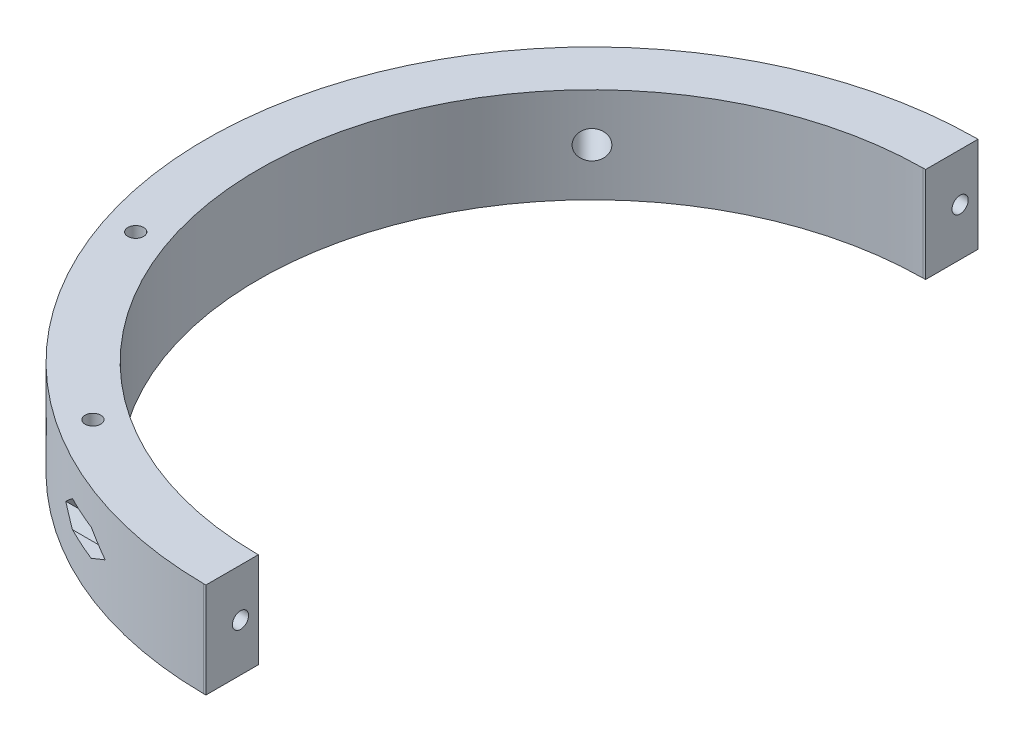
SolidWorks part; units mm, degrees
ref_plane "Front Plane" through (0, 0, 0) normal (0, 0, 1) x (1, 0, 0)
ref_plane "Top Plane" through (0, 0, 0) normal (0, 1, 0) x (1, 0, 0)
ref_plane "Right Plane" through (0, 0, 0) normal (1, 0, 0) x (0, 0, -1)
sketch "Sketch1" plane through (0, 0, 0) normal (0, 1, 0) x (1, 0, 0)
  line L0 (0, 70) -> (0, 81)
  line L1 (0, -70) -> (0, -81)
  circle A0 centre (0, 0) radius 70 construction
  arc A1 (0, 70) -> (0, -70) centre (0, 0) ccw
  arc A2 (0, -81) -> (0, 81) centre (0, 0) cw
  dimension "D1" = 140
  dimension "D2" = 11
extrude "Boss-Extrude1" add sketch "Sketch1" along normal mid plane 20 contours A1 L1 A2 L0
sketch "Sketch2" plane through (0, 0, 0) normal (1, 0, 0) x (0, 0, -1)
  line L1 (-81, 10) -> (81, 10)
  line L2 (-81, 10) -> (-81, -10)
  line L3 (-81, -10) -> (81, -10)
  line L4 (81, 10) -> (81, -10)
  line L5 (-81, 10) -> (81, -10) construction
  line L6 (-81, -10) -> (81, 10) construction
  point P0 (0, 0)
extrude "Cut-Extrude1" cut sketch "Sketch2" against normal blind 0.5
ref_plane "Plane1" through (-75, 0, 0) normal (1, 0, 0) x (0, 0, -1)
sketch "Sketch4" plane through (-75, 0, 0) normal (1, 0, 0) x (0, 0, -1)
  line L0 (44.55, 0) -> (-44.55, 0) construction
  line L1 (-72.1172, 2.825) -> (-75.3792, 2.825)
  line L2 (-75.3792, 2.825) -> (-77.0102, 0)
  line L3 (-77.0102, 0) -> (-75.3792, -2.825)
  line L4 (-75.3792, -2.825) -> (-72.1172, -2.825)
  line L5 (-72.1172, -2.825) -> (-70.4862, 0)
  line L6 (-70.4862, 0) -> (-72.1172, 2.825)
  line L8 (80.5105, 0) -> (78.8795, 2.825)
  line L9 (78.8795, 2.825) -> (75.6174, 2.825)
  line L10 (75.6174, 2.825) -> (73.9864, 0)
  line L11 (73.9864, 0) -> (75.6174, -2.825)
  line L12 (75.6174, -2.825) -> (78.8795, -2.825)
  line L13 (78.8795, -2.825) -> (80.5105, 0)
  line L14 (-69.9982, 10) -> (-69.9982, -10) construction
  line L16 (80.9985, 10) -> (80.9985, -10) construction
  circle A0 centre (-73.7482, 0) radius 2.825 construction
  circle A1 centre (77.2485, 0) radius 2.825 construction
  dimension "D1" = 5.65
  dimension "D2" = 3.75
  dimension "D3" = 3.75
extrude "Cut-Extrude2" cut sketch "Sketch4" along normal blind 67.5
hole_wizard "CBORE for M3 SHCS1" [suppressed] positions "Sketch6" profile "Sketch8" counterbore size "M3" standard "ANSI Metric"
sketch "Sketch6" [suppressed] plane through (-75, 0, 0) normal (1, 0, 0) x (0, 0, -1)
  line L0 (44.55, 0) -> (-44.55, 0) construction
  line L1 (-80.9985, -10) -> (-80.9985, 10) construction
  line L2 (80.9985, 10) -> (80.9985, -10) construction
  point P0 (-77.2485, 0)
  point P4 (77.2485, 0)
  dimension "D1" = 3.75
  dimension "D2" = 3.75
sketch "Sketch8" plane through (-75, 0, 77.2485) normal (0, 1, 0) x (0, 0, 1)
  line L0 (0, 0) -> (0, 95.5215)
  line L1 (0, 95.5215) -> (1.7, 94.5)
  line L2 (1.7, 94.5) -> (1.7, 67.5)
  line L3 (1.7, 67.5) -> (3.25, 67.5)
  line L4 (3.25, 67.5) -> (3.25, 0)
  line L5 (3.25, 0) -> (0, 0)
  line L10 (0, 95.5215) -> (-1.7, 94.5) construction
  line L11 (0, -6.35) -> (0, 107.95) construction
  dimension "Hole Dia." = 3.4
  dimension "Hole Depth" = 94.5
  dimension "C'Bore Dia." = 6.5
  dimension "C'Bore Depth" = 67.5
  dimension "Drill Angle" = 118
ref_plane "Plane2" through (-57.2756, 0, -57.2756) normal (-0.7071, 0, -0.7071) x (0, -1, 0)
ref_plane "Plane3" through (-57.2756, 0, 57.2756) normal (-0.7071, 0, 0.7071) x (0, -1, 0)
ref_plane "Plane4" through (0, 0, 0) normal (0.7071, 0, -0.7071) x (-0.7071, 0, -0.7071)
ref_plane "Plane5" through (0, 0, 0) normal (0.7071, 0, 0.7071) x (0.7071, 0, -0.7071)
ref_plane "Plane6" through (-49.4975, 0, -49.4975) normal (0.7071, 0, 0.7071) x (0, -1, 0)
hole_wizard "CBORE for M3 Pan Head Machine Screw4" [suppressed] positions "Sketch11" profile "Sketch12" counterbore size "M3" standard "ANSI Metric"
sketch "Sketch11" plane through (0, 0, 0) normal (0.7071, 0, 0.7071) x (0.7071, 0, -0.7071)
  point P0 (0, 0)
sketch "Sketch12" plane through (0, 0, 0) normal (0, 1, 0) x (0.7071, 0, -0.7071)
  line L0 (0, 0) -> (0, 114.5502)
  line L1 (0, 114.5502) -> (1.6, 114.5502)
  line L3 (1.6, 114.5502) -> (1.6, 73)
  line L4 (1.6, 73) -> (3.5, 73)
  line L5 (3.5, 73) -> (3.5, 0)
  line L7 (3.5, 0) -> (0, 0)
  line L11 (0, -6.35) -> (0, 107.95) construction
  dimension "Thru Hole Dia." = 3.2
  dimension "Thru Hole Depth" = 114.5502
  dimension "C'Bore Dia." = 7
  dimension "C'Bore Depth" = 73
sketch "Sketch15" [suppressed] plane through (-57.2756, 0, -57.2756) normal (-0.7071, 0, -0.7071) x (0, -1, 0)
  line L0 (0, -5.85) -> (0, 2761.2985) construction
  line L1 (-0.5, -5.85) -> (-4.25, -5.85)
  line L2 (-4.25, -5.85) -> (-6.95, 1.8)
  line L3 (-0.5, -5.85) -> (-0.5, -1) construction
  line L4 (-0.5, 1) -> (-0.5, 2.63) construction
  line L5 (0, 3.13) -> (0, 37.67)
  line L6 (-6.95, 1.8) -> (-4.4104, 32.0511)
  line L7 (0, 3.13) -> (0, -5.85)
  line L8 (0, -5.85) -> (-0.5, -5.85)
  arc A0 (-0.5, -1) -> (-0.5, 1) centre (-0.5, 0) cw construction
  arc A1 (-0.5, 2.63) -> (0, 3.13) centre (0, 2.63) cw construction
  arc A2 (-4.4104, 32.0511) -> (0, 37.67) centre (2.0668, 31.5074) cw
extrude "Cut-Extrude4" [suppressed] cut sketch "Sketch15" against normal blind 6
mirror "Mirror1" [suppressed] about plane through (0, 0, 0) normal (0, 1, 0)
hole_wizard "Ø6.0mm Dowel Hole2" positions "Sketch18" profile "Sketch19" hole size "Ø6.0" standard "ANSI Metric" end condition through all
sketch "Sketch18" plane through (0, 0, 0) normal (0.7071, 0, -0.7071) x (-0.7071, 0, -0.7071)
  point P0 (0, 0)
sketch "Sketch19" plane through (0, 0, 0) normal (0, 1, 0) x (-0.7071, 0, -0.7071)
  line L0 (0, 0) -> (0, 114.5502)
  line L1 (0, 114.5502) -> (2.95, 114.5502)
  line L2 (2.95, 114.5502) -> (2.95, 0)
  line L5 (2.95, 0) -> (0, 0)
  line L11 (0, -6.35) -> (0, 107.95) construction
  dimension "Thru Hole Dia." = 5.9
  dimension "Thru Hole Depth" = 114.5502
hole_wizard "Ø6.0mm Dowel Hole3" [suppressed] positions "Sketch20" profile "Sketch21" hole size "Ø6.0" standard "ANSI Metric"
sketch "Sketch20" plane through (0, 0, 0) normal (0.7071, 0, -0.7071) x (-0.7071, 0, -0.7071)
  point P0 (0, 0)
sketch "Sketch21" plane through (0, 0, 0) normal (0, 1, 0) x (-0.7071, 0, -0.7071)
  line L0 (0, 0) -> (0, 114.5502)
  line L1 (0, 114.5502) -> (2.95, 114.5502)
  line L2 (2.95, 114.5502) -> (2.95, 0)
  line L5 (2.95, 0) -> (0, 0)
  line L11 (0, -6.35) -> (0, 107.95) construction
  dimension "Thru Hole Dia." = 5.9
  dimension "Thru Hole Depth" = 114.5502
hole_wizard "Ø6.0mm Dowel Hole4" positions "Sketch22" profile "Sketch23" hole size "Ø6.0" standard "ANSI Metric" end condition through all
sketch "Sketch22" plane through (0, 0, 0) normal (0.7071, 0, 0.7071) x (0.7071, 0, -0.7071)
  point P0 (0, 0)
sketch "Sketch23" plane through (0, 0, 0) normal (0, 1, 0) x (0.7071, 0, -0.7071)
  line L0 (0, 0) -> (0, 114.5502)
  line L1 (0, 114.5502) -> (2.95, 114.5502)
  line L2 (2.95, 114.5502) -> (2.95, 0)
  line L5 (2.95, 0) -> (0, 0)
  line L11 (0, -6.35) -> (0, 107.95) construction
  dimension "Thru Hole Dia." = 5.9
  dimension "Thru Hole Depth" = 114.5502
sketch "Sketch25" plane through (0, 0, 0) normal (0.7071, 0, 0.7071) x (0.7071, 0, -0.7071)
  line L0 (0, 0) -> (34.3178, 9.1954)
  line L1 (44.55, 0) -> (-44.55, 0) construction
  line L2 (0, -55) -> (0, 55) construction
  line L3 (0, 0) -> (-34.3178, 9.1954)
  dimension "D1" = 15
sketch "Sketch30" plane through (0, -10, 0) normal (0, -1, 0) x (1, 0, 0)
  line L0 (0, 0) -> (-49.4975, 49.4975) construction
  line L1 (0, 0) -> (0, 40.1385) construction
  circle A0 centre (0, 0) radius 75.5 construction
  arc A1 (-0.5, 69.9982) -> (-0.5, -69.9982) centre (0, 0) ccw construction
  circle A2 centre (-41.8941, 62.8103) radius 1.65
  circle A3 centre (-71.5137, 24.2083) radius 1.65
  point P1 (-41.8941, 62.8103)
  point P4 (-71.5137, 24.2083)
  dimension "D1" = 151
  dimension "D5" = 3.3
  dimension "D2" = 14.79
  dimension "D3" = 33.45
  dimension "D4" = 45
extrude "Cut-Extrude7" cut sketch "Sketch30" against normal mid plane 40
sketch "Sketch31" plane through (-0.5, 0, 0) normal (1, 0, 0) x (0, 0, -1)
  line L0 (-69.9982, 10) -> (-69.9982, -10)
  line L1 (-80.9985, -10) -> (-69.9982, -10)
  line L2 (-80.9985, -10) -> (-80.9985, 10)
  line L3 (-80.9985, 10) -> (-69.9982, 10)
  line L4 (80.9985, -10) -> (80.9985, 10)
  line L7 (69.9982, 10) -> (69.9982, -10)
  line L8 (69.9982, -10) -> (80.9985, -10)
  line L11 (69.9982, 10) -> (80.9985, 10)
  point P0 (0, 0)
extrude "Boss-Extrude2" add sketch "Sketch31" along normal blind 0.5
sketch "Sketch5" plane through (-75, 0, 0) normal (1, 0, 0) x (0, 0, -1)
  line L0 (44.55, 0) -> (-44.55, 0) construction
  line L5 (-75.3792, 2.825) -> (-72.1172, 2.825) construction
  line L6 (75.6174, 2.825) -> (78.8795, 2.825) construction
  circle A0 centre (77.2485, 0) radius 1.7
  circle A1 centre (-73.7482, 0) radius 1.7
  point P9 (-73.7482, 2.825)
  point P12 (77.2485, 2.825)
  dimension "D1" = 3.4
sketch "Sketch32" [suppressed] plane through (0, 0, 0) normal (1, 0, 0) x (0, 0, -1)
  circle A0 centre (-77.2485, 0) radius 1.7
  circle A1 centre (77.2485, 0) radius 1.7
extrude "Cut-Extrude10" [suppressed] cut sketch "Sketch32" along normal mid plane 20.5
extrude "Cut-Extrude3" cut sketch "Sketch5" along normal mid plane 230
